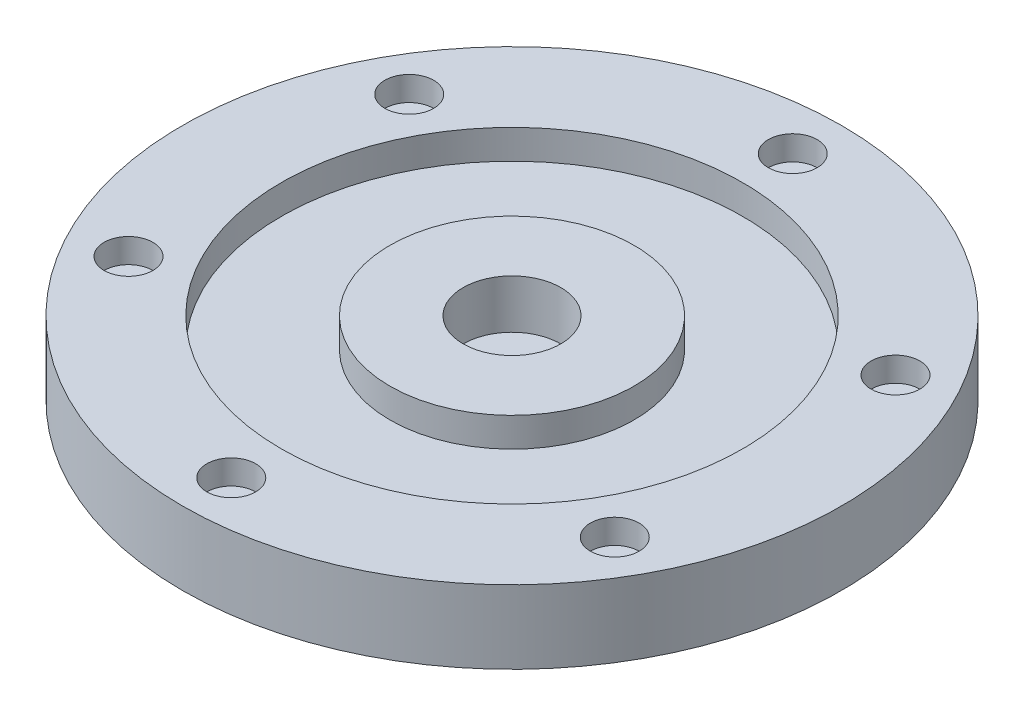
SolidWorks part; units mm, degrees
material "ABS"
ref_plane "Front Plane" through (0, 0, 0) normal (0, 0, 1) x (1, 0, 0)
ref_plane "Top Plane" through (0, 0, 0) normal (0, 1, 0) x (1, 0, 0)
ref_plane "Right Plane" through (0, 0, 0) normal (1, 0, 0) x (0, 0, -1)
sketch "Sketch1" plane through (0, 0, 0) normal (0, 1, 0) x (1, 0, 0)
  circle A0 centre (0, 0) radius 67.5
  dimension "D1" = 135
extrude "Boss-Extrude1" add sketch "Sketch1" along normal blind 15
sketch "Sketch2" plane through (0, 15, 0) normal (0, 1, 0) x (1, 0, 0)
  circle A0 centre (0, 0) radius 47.25
  circle A1 centre (0, 0) radius 25
  dimension "D1" = 94.5
  dimension "D2" = 50
extrude "Cut-Extrude1" cut sketch "Sketch2" against normal blind 6
sketch "Sketch3" plane through (0, 15, 0) normal (0, 1, 0) x (1, 0, 0)
  circle A0 centre (0, 0) radius 10
  dimension "D1" = 20
extrude "Cut-Extrude2" cut sketch "Sketch3" against normal blind 10
sketch "Sketch5" plane through (0, 5, 0) normal (0, 1, 0) x (1, 0, 0)
  circle A0 centre (0, 0) radius 2.5
  dimension "D1" = 5
extrude "Cut-Extrude3" cut sketch "Sketch5" against normal blind 10
sketch "Sketch6" plane through (0, 15, 0) normal (0, 1, 0) x (1, 0, 0)
  circle A0 centre (0, 0) radius 57.5 construction
  circle A1 centre (0, 57.5) radius 2
  circle A2 centre (49.7965, 28.75) radius 2
  circle A3 centre (49.7965, -28.75) radius 2
  circle A4 centre (0, -57.5) radius 2
  circle A5 centre (-49.7965, -28.75) radius 2
  circle A6 centre (-49.7965, 28.75) radius 2
  point P17 (0, 0)
  dimension "D1" = 115
  dimension "D2" = 4
  dimension "D3" = 6
extrude "Cut-Extrude4" cut sketch "Sketch6" against normal blind 15
sketch "Sketch7" plane through (0, 15, 0) normal (0, 1, 0) x (1, 0, 0)
  circle A0 centre (0, 57.5) radius 5
  circle A1 centre (49.7965, 28.75) radius 5
  circle A2 centre (49.7965, -28.75) radius 5
  circle A3 centre (0, -57.5) radius 5
  circle A4 centre (-49.7965, -28.75) radius 5
  circle A5 centre (-49.7965, 28.75) radius 5
  point P15 (0, 0)
  dimension "D1" = 10
  dimension "D2" = 6
extrude "Cut-Extrude5" cut sketch "Sketch7" against normal blind 5
